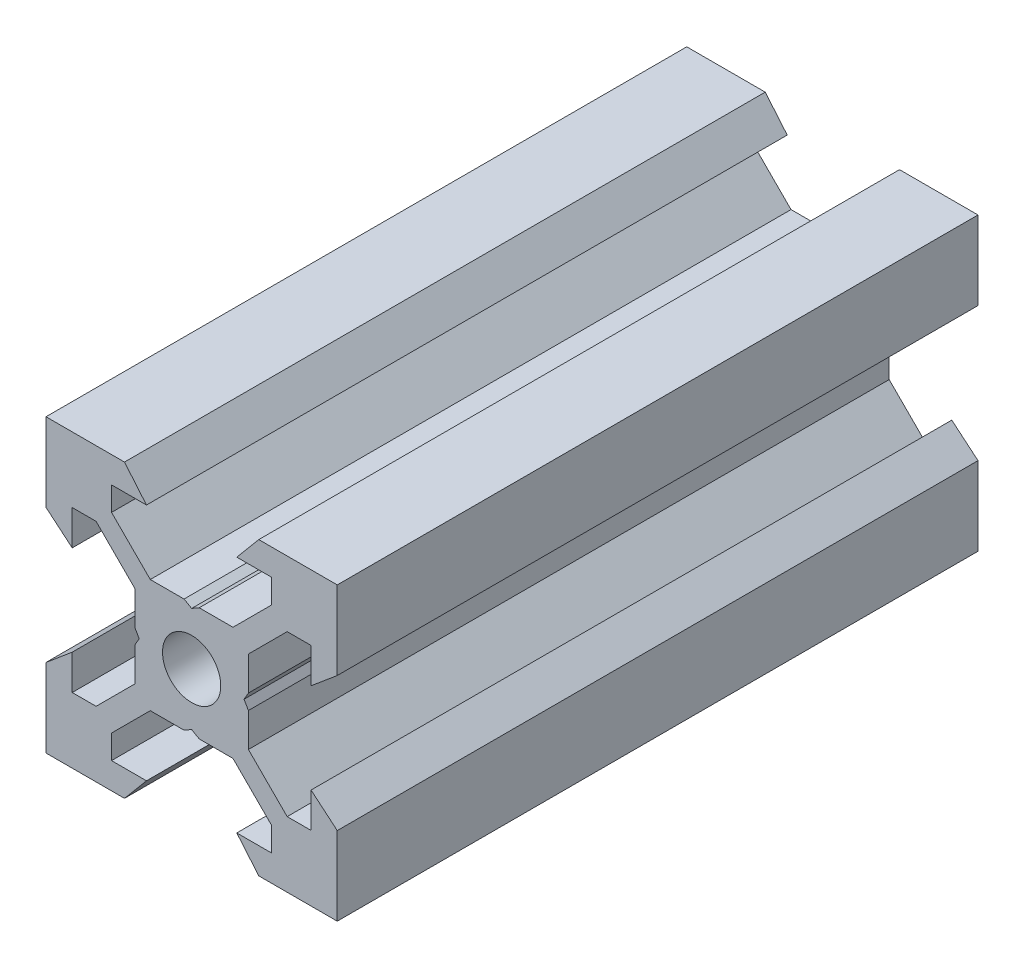
SolidWorks part; units mm, degrees
ref_plane "Front Plane" through (0, 0, 0) normal (0, 0, 1) x (1, 0, 0)
ref_plane "Top Plane" through (0, 0, 0) normal (0, 1, 0) x (1, 0, 0)
ref_plane "Right Plane" through (0, 0, 0) normal (1, 0, 0) x (0, 0, -1)
sketch "Sketch1" plane through (0, 0, 0) normal (0, 0, 1) x (1, 0, 0)
  line L0 (10, 10) -> (4.6104, 10) construction
  line L1 (10, 10) -> (10, 4.6104) construction
  line L2 (10, -10) -> (10, -4.6104) construction
  line L3 (10, -10) -> (4.6104, -10) construction
  line L4 (10, 10) -> (10, 4.6104)
  line L5 (6.5607, 5.5) -> (8.2, 5.5)
  line L6 (5.5, 8.2) -> (5.5, 6.5607)
  line L7 (10, 10) -> (4.6104, 10)
  line L8 (10, 10) -> (10, 4.6104)
  line L9 (6.5607, 5.5) -> (3.9, 2.8393)
  line L10 (5.5, 6.5607) -> (2.8393, 3.9)
  line L11 (10, 4.6104) -> (8.2, 3.1)
  line L12 (4.6104, 10) -> (3.1, 8.2)
  line L13 (8.2, 3.1) -> (8.2, 5.5)
  line L14 (3.1, 8.2) -> (5.5, 8.2)
  line L15 (-6.5607, 5.5) -> (-8.2, 5.5)
  line L16 (6.5607, -5.5) -> (8.2, -5.5)
  line L17 (3.1, -8.2) -> (5.5, -8.2)
  line L18 (8.2, -3.1) -> (8.2, -5.5)
  line L19 (4.6104, -10) -> (3.1, -8.2)
  line L20 (10, -4.6104) -> (8.2, -3.1)
  line L21 (0.5196, -3.9) -> (0, -3.6)
  line L22 (0.5196, 3.9) -> (0, 3.6)
  line L23 (3.6, 0) -> (3.9, -0.5196)
  line L24 (3.9, 0.5196) -> (3.6, 0)
  line L25 (3.9, 0.5196) -> (3.9, 2.8393)
  line L26 (2.8393, 3.9) -> (0.5196, 3.9)
  line L27 (3.9, -2.8393) -> (3.9, -0.5196)
  line L28 (2.8393, -3.9) -> (0.5196, -3.9)
  line L29 (5.5, -6.5607) -> (2.8393, -3.9)
  line L30 (6.5607, -5.5) -> (3.9, -2.8393)
  line L31 (10, -10) -> (10, -4.6104)
  line L32 (10, -10) -> (4.6104, -10)
  line L33 (5.5, -8.2) -> (5.5, -6.5607)
  line L34 (-6.5607, -5.5) -> (-8.2, -5.5)
  line L35 (10, -10) -> (10, -4.6104)
  line L36 (0, 0) -> (0, 8.2) construction
  line L37 (-10, -10) -> (-4.6104, -10) construction
  line L38 (-10, -10) -> (-10, -4.6104) construction
  line L39 (-10, 10) -> (-10, 4.6104) construction
  line L40 (-10, 10) -> (-4.6104, 10) construction
  line L41 (-10, -10) -> (-10, -4.6104)
  line L43 (-5.5, -8.2) -> (-5.5, -6.5607)
  line L44 (-10, -10) -> (-4.6104, -10)
  line L45 (-10, -10) -> (-10, -4.6104)
  line L46 (-6.5607, -5.5) -> (-3.9, -2.8393)
  line L47 (-5.5, -6.5607) -> (-2.8393, -3.9)
  line L48 (-2.8393, -3.9) -> (-0.5196, -3.9)
  line L49 (-3.9, -2.8393) -> (-3.9, -0.5196)
  line L50 (-2.8393, 3.9) -> (-0.5196, 3.9)
  line L51 (-3.9, 0.5196) -> (-3.9, 2.8393)
  line L52 (-3.9, 0.5196) -> (-3.6, 0)
  line L53 (-3.6, 0) -> (-3.9, -0.5196)
  line L54 (-0.5196, 3.9) -> (0, 3.6)
  line L55 (-0.5196, -3.9) -> (0, -3.6)
  line L56 (-10, -4.6104) -> (-8.2, -3.1)
  line L57 (-4.6104, -10) -> (-3.1, -8.2)
  line L58 (-8.2, -3.1) -> (-8.2, -5.5)
  line L59 (-3.1, -8.2) -> (-5.5, -8.2)
  line L60 (-10, -10) -> (10, -10) construction
  line L61 (-10, -10) -> (-10, 10) construction
  line L62 (-3.1, 8.2) -> (-5.5, 8.2)
  line L63 (-8.2, 3.1) -> (-8.2, 5.5)
  line L64 (-4.6104, 10) -> (-3.1, 8.2)
  line L65 (-10, 4.6104) -> (-8.2, 3.1)
  line L66 (-5.5, 6.5607) -> (-2.8393, 3.9)
  line L67 (-6.5607, 5.5) -> (-3.9, 2.8393)
  line L68 (-10, 10) -> (-10, 4.6104)
  line L69 (-10, 10) -> (-4.6104, 10)
  line L70 (-5.5, 8.2) -> (-5.5, 6.5607)
  line L71 (-10, 10) -> (10, 10) construction
  line L72 (-10, 10) -> (-10, 4.6104)
  line L73 (10, -10) -> (10, 10) construction
  line L74 (-10, -10) -> (10, 10) construction
  line L75 (-10, 10) -> (10, -10) construction
  circle A0 centre (0, 0) radius 2
  dimension "D7" = 4
  dimension "D1" = 20
  dimension "D2" = 5.3896
  dimension "D3" = 4.5
  dimension "D4" = 50
  dimension "D5" = 1.8
  dimension "D6" = 1.5104
  dimension "D8" = 5.5
  dimension "D9" = 120
  dimension "D10" = 0.3
  dimension "D11" = 2.3197
  dimension "D12" = 7.8
  dimension "D13" = 7.8
  dimension "D14" = 1.5
  dimension "D15" = 2.6607
extrude "Boss-Extrude1" add sketch "Sketch1" along normal mid plane 44 contours L70 L62 L64 L69 L68 L65 L63 L15 L67 L51 L52 L53 L49 L46 L34 L58 L56 L41 L44 L57 L59 L43 L47 L48 L55 L21 L28 L29 L33 L17 L19 L32 L31 L20 L18 L16 L30 L27 L23 L24 L25 L9 L5 L13 L11 L4 L7 L12 L14 L6 L10
